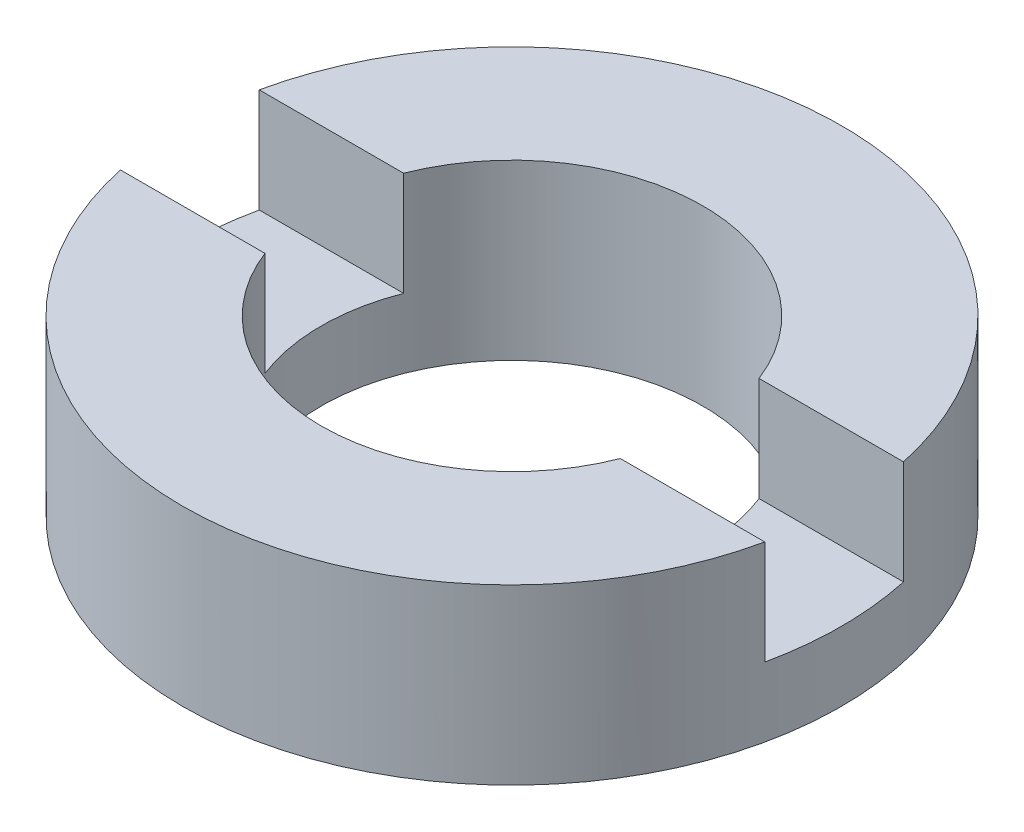
SolidWorks part; units mm, degrees
ref_plane "前视基准面" through (0, 0, 0) normal (0, 0, 1) x (1, 0, 0)
ref_plane "上视基准面" through (0, 0, 0) normal (0, 1, 0) x (1, 0, 0)
ref_plane "右视基准面" through (0, 0, 0) normal (1, 0, 0) x (0, 0, -1)
sketch "草图1" plane through (0, 0, 0) normal (0, 0, 1) x (1, 0, 0)
  line L0 (0, 56.2608) -> (0, -99.1922) construction
  line L1 (2.75, -1.9642) -> (4.75, -1.9642)
  line L4 (4.75, -1.9642) -> (4.75, -4.4642)
  line L5 (2.75, -4.4642) -> (2.75, -1.9642)
  line L7 (2.75, -4.4642) -> (4.75, -4.4642)
  dimension "D1" = 2.5
  dimension "D2" = 4.75
  dimension "D3" = 2.75
revolve "旋转1" add sketch "草图1" angle 360 about L0
cosmetic thread "装饰螺纹线1" parameters "D2"=8.5
sketch "草图2" plane through (0, -1.9642, 0) normal (0, 1, 0) x (1, 0, 0)
  line L0 (-28.67, 0) -> (29.9422, 0) construction
  line L2 (-26.8525, 1) -> (26.8525, 1)
  line L3 (-26.8525, 1) -> (-26.8525, -1)
  line L4 (-26.8525, -1) -> (26.8525, -1)
  line L5 (26.8525, 1) -> (26.8525, -1)
  line L6 (-26.8525, 1) -> (26.8525, -1) construction
  line L7 (-26.8525, -1) -> (26.8525, 1) construction
  point P3 (0, 0)
  dimension "D1" = 2
extrude "切除-拉伸1" cut sketch "草图2" against normal blind 1.5
